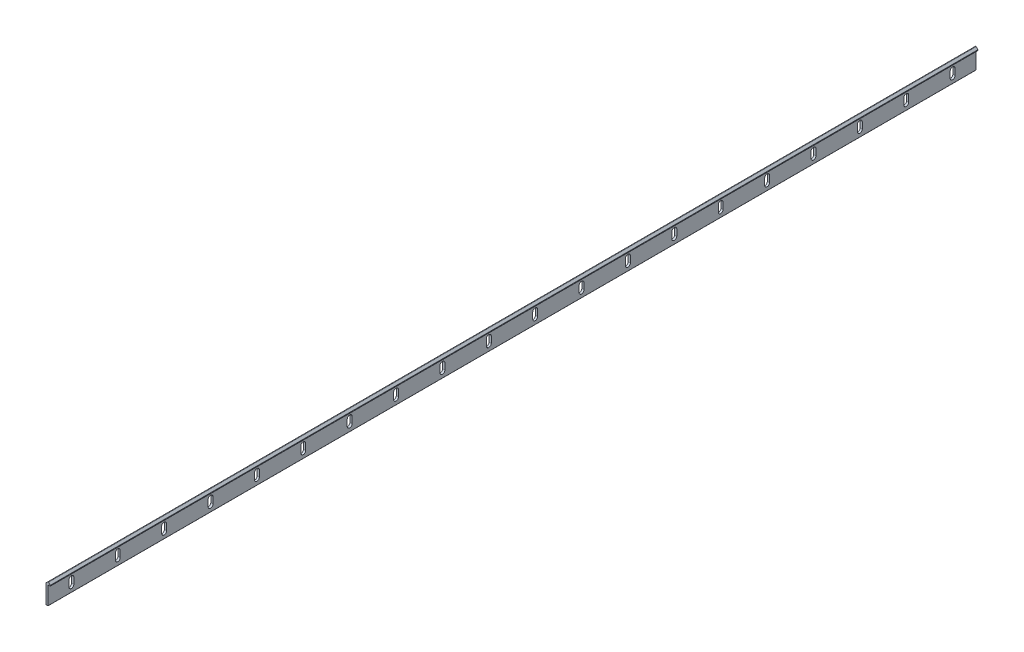
SolidWorks part; units mm, degrees
ref_plane "Front Plane" through (0, 0, 0) normal (0, 0, 1) x (1, 0, 0)
ref_plane "Top Plane" through (0, 0, 0) normal (0, 1, 0) x (1, 0, 0)
ref_plane "Right Plane" through (0, 0, 0) normal (1, 0, 0) x (0, 0, -1)
sketch "Sketch1" plane through (0, 0, 0) normal (0, 0, 1) x (1, 0, 0)
  line L0 (0, 20.3302) -> (2.0196, 22.3498)
  line L1 (0, 0) -> (2.375, 0)
  line L2 (0, 20.3302) -> (0, 0)
  line L4 (2.375, 0) -> (2.375, 19.5291)
  line L5 (2.375, 19.5291) -> (4.75, 19.5291)
  line L7 (2.7304, 22.3498) -> (4.75, 20.3302)
  line L8 (4.75, 19.5291) -> (4.75, 20.3302)
  arc A0 (2.7304, 22.3498) -> (2.0196, 22.3498) centre (2.375, 21.9944) ccw
  point P9 (2.375, 22.7052)
  dimension "D5" = 0.5026
  dimension "D6" = 22.497
  dimension "D1" = 2.375
  dimension "D2" = 19.5291
  dimension "D3" = 2.375
  dimension "D4" = 2.9679
extrude "Boss-Extrude1" add sketch "Sketch1" along normal blind 1000
fillet "Fillet1" radius 0.5033 1 edges at (0, 20.3302, 500)
fillet "Fillet2" radius 0.504 1 edges at (4.75, 20.3302, 500)
fillet "Fillet3" radius 0.3016 1 edges at (4.75, 19.5291, 500)
fillet "Fillet4" radius 0.3016 2 edges at (0, 0, 500) (2.375, 0, 500)
sketch "Sketch2" plane through (0, 0, 0) normal (-1, 0, 0) x (0, 0, 1)
  line L0 (25, 13.1043) -> (25, 6.4043) construction
  line L1 (27.65, 13.1043) -> (27.65, 6.4043)
  line L2 (22.35, 13.1043) -> (22.35, 6.4043)
  line L3 (1000, 0) -> (0, 0) construction
  line L4 (0, 20.1217) -> (0, 0.3016) construction
  arc A0 (27.65, 13.1043) -> (22.35, 13.1043) centre (25, 13.1043) ccw
  arc A1 (22.35, 6.4043) -> (27.65, 6.4043) centre (25, 6.4043) ccw
  point P2 (25, 9.7543)
  dimension "D3" = 9.7543
  dimension "D1" = 5.3
  dimension "D2" = 6.7
  dimension "D4" = 25
extrude "Cut-Extrude1" cut sketch "Sketch2" against normal up to next (2.375 mm away)
pattern_linear "LPattern1" count 20 spacing 50 along (0, 0, 1) of "Cut-Extrude1"
equation "\"D3@Sketch1\"=\"D1@Sketch1\""
